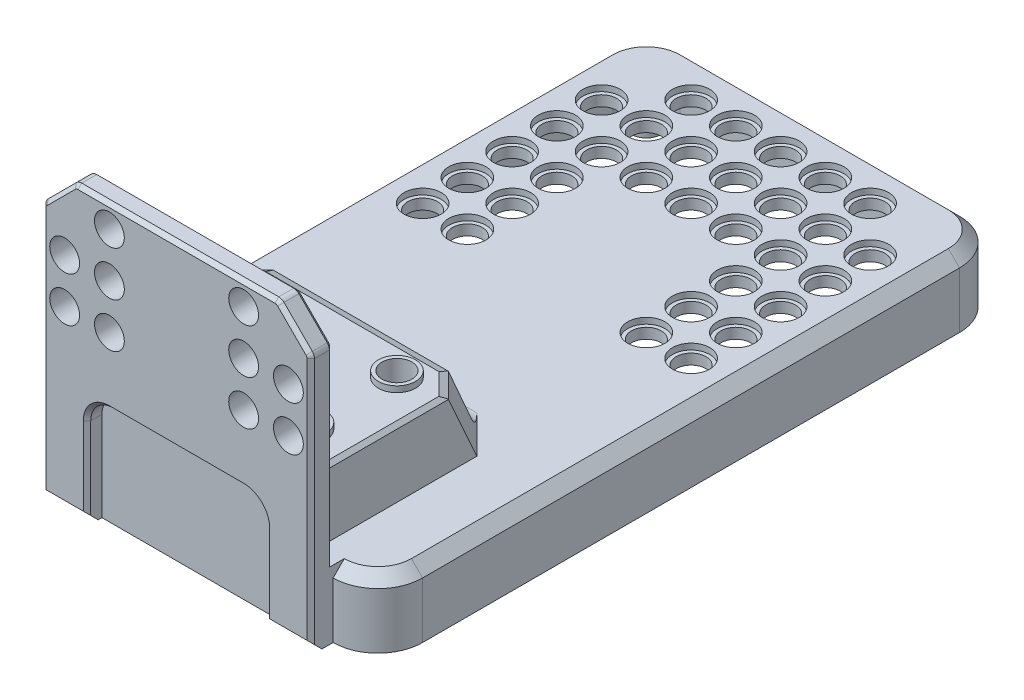
SolidWorks part; units mm, degrees
material "ABS"
ref_plane "Front Plane" through (0, 0, 0) normal (0, 0, 1) x (1, 0, 0)
ref_plane "Top Plane" through (0, 0, 0) normal (0, 1, 0) x (1, 0, 0)
ref_plane "Right Plane" through (0, 0, 0) normal (1, 0, 0) x (0, 0, -1)
sketch "Sketch1" plane through (0, 0, 0) normal (0, 1, 0) x (1, 0, 0)
  line L0 (-24, 36) -> (-24, -36)
  line L1 (-18, -42) -> (18, -42)
  line L2 (-18, 42) -> (18, 42)
  line L3 (0, -1000) -> (0, 49000) construction
  line L4 (24, 36) -> (24, -36)
  arc A0 (-24, -36) -> (-18, -42) centre (-18, -36) ccw
  arc A1 (-24, 36) -> (-18, 42) centre (-18, 36) cw
  arc A2 (24, 36) -> (18, 42) centre (18, 36) ccw
  arc A3 (24, -36) -> (18, -42) centre (18, -36) cw
  point P7 (-24, 0)
  point P9 (0, -42)
  point P18 (0, 42)
  dimension "D1" = 6
  dimension "D2" = 72
  dimension "D3" = 18
extrude "Boss-Extrude1" add sketch "Sketch1" along normal mid plane 2.2
sketch "Sketch2" plane through (0, -1.1, 0) normal (0, -1, 0) x (1, 0, 0)
  line L0 (24, 36) -> (24, -36) construction
  line L1 (18, -42) -> (-18, -42) construction
  line L2 (-24, -36) -> (-24, 36) construction
  line L3 (-18, 42) -> (18, 42) construction
  line L4 (24, 36) -> (24, -36)
  line L5 (18, -42) -> (-18, -42)
  line L6 (-24, -36) -> (-24, 36)
  line L7 (-18, 42) -> (18, 42)
  line L8 (18, -40.5) -> (-18, -40.5)
  line L9 (-22.5, -36) -> (-22.5, 36)
  line L10 (-18, 40.5) -> (18, 40.5)
  line L11 (22.5, 36) -> (22.5, -36)
  arc A0 (24, 36) -> (18, 42) centre (18, 36) ccw construction
  arc A1 (18, -42) -> (24, -36) centre (18, -36) ccw construction
  arc A2 (-24, -36) -> (-18, -42) centre (-18, -36) ccw construction
  arc A3 (-18, 42) -> (-24, 36) centre (-18, 36) ccw construction
  arc A4 (24, 36) -> (18, 42) centre (18, 36) ccw
  arc A5 (18, -42) -> (24, -36) centre (18, -36) ccw
  arc A6 (-24, -36) -> (-18, -42) centre (-18, -36) ccw
  arc A7 (-18, 42) -> (-24, 36) centre (-18, 36) ccw
  arc A8 (-18, -40.5) -> (-22.5, -36) centre (-18, -36) cw
  arc A9 (-22.5, 36) -> (-18, 40.5) centre (-18, 36) cw
  arc A10 (18, 40.5) -> (22.5, 36) centre (18, 36) cw
  arc A11 (22.5, -36) -> (18, -40.5) centre (18, -36) cw
  dimension "D1" = 1.5
extrude "Boss-Extrude2" add sketch "Sketch2" along normal blind 6.8
sketch "Sketch4" plane through (0, -1.1, 0) normal (0, -1, 0) x (1, 0, 0)
  line L1 (-18, 42) -> (18, 42) construction
  line L3 (15, 18.75) -> (12, 15.75)
  line L4 (12, 15.75) -> (-12, 15.75)
  line L5 (-12, 15.75) -> (-15, 18.75)
  line L8 (-15, 18.75) -> (-15, 42)
  line L9 (-15, 42) -> (15, 42)
  line L10 (15, 42) -> (15, 18.75)
  point P4 (0, 42)
  point P9 (0, 15.75)
  dimension "D1" = 30
  dimension "D2" = 24
  dimension "D3" = 23.25
ref_plane "Plane1" through (0, 10.1, 0) normal (0, -1, 0) x (-1, 0, 0)
sketch "Sketch5" plane through (0, 10.1, 0) normal (0, -1, 0) x (-1, 0, 0)
  line L0 (-15, -42) -> (15, -42)
  line L1 (-15, -42) -> (-15, -23.75)
  line L2 (-15, -42) -> (-15, -18.75) construction
  line L3 (-15, -23.75) -> (-11.75, -20.5)
  line L4 (-11.75, -20.5) -> (11.75, -20.5)
  line L5 (11.75, -20.5) -> (15, -23.75)
  line L6 (15, -18.75) -> (15, -42) construction
  line L7 (15, -23.75) -> (15, -42)
  line L8 (-15, -18.75) -> (-12, -15.75) construction
  line L9 (12, -15.75) -> (15, -18.75) construction
  point P16 (0, -20.5)
  point P17 (0, -42)
  dimension "D1" = 23.5
  dimension "D2" = 18.25
loft "Loft1" add profiles "Sketch4", "Sketch5"
sketch "Sketch6" plane through (0, 0, 42) normal (0, 0, 1) x (1, 0, 0)
  line L0 (18, -7.9) -> (-18, -7.9)
  line L1 (18, -7.9) -> (18, 26.725)
  line L2 (18, 26.725) -> (13.625, 31.1)
  line L3 (13.625, 31.1) -> (-13.625, 31.1)
  line L4 (-13.625, 31.1) -> (-18, 26.725)
  line L5 (-18, 26.725) -> (-18, -7.9)
  point P4 (0, 31.1)
  point P9 (0, -7.9)
  dimension "D1" = 39
  dimension "D2" = 27.25
extrude "Boss-Extrude3" add sketch "Sketch6" along normal blind 3
fillet "Fillet1" radius 1 4 edges at (-18, 26.725, 43.5) (-13.625, 31.1, 43.5) (18, 26.725, 43.5) (13.625, 31.1, 43.5)
ref_plane "Plane2" through (0, 7.9, 0) normal (0, -1, 0) x (-1, 0, 0)
sketch "Sketch7" plane through (0, 7.9, 0) normal (0, -1, 0) x (-1, 0, 0)
  line L7 (13.5, -42) -> (-13.5, -42)
  line L11 (-15, -42) -> (15, -42) construction
  line L12 (-13.2108, -42) -> (13.2108, -42) construction
  line L13 (-13.5, -42) -> (-13.5, -24.3713)
  line L14 (-13.5, -24.3713) -> (-11.1287, -22)
  line L15 (-11.1287, -22) -> (11.1287, -22)
  line L16 (11.1287, -22) -> (13.5, -24.3713)
  line L17 (13.5, -24.3713) -> (13.5, -42)
  line L18 (11.75, -20.5) -> (-11.75, -20.5) construction
  line L19 (15, -23.75) -> (11.75, -20.5) construction
  point P7 (0, -22)
  point P13 (0, -42)
  point P19 (13.375, -22.125)
  dimension "D1" = 27
  dimension "D2" = 1.5
  dimension "D3" = 1.5
sketch "Sketch8" plane through (0, -1.1, 0) normal (0, -1, 0) x (1, 0, 0)
  line L0 (13.5, 42) -> (-13.5, 42)
  line L1 (-13.5, 42) -> (-13.5, 19)
  line L2 (-13.5, 19) -> (-11.1287, 16.6287)
  line L3 (-11.1287, 16.6287) -> (11.1287, 16.6287)
  line L4 (11.1287, 16.6287) -> (13.5, 19)
  line L5 (13.5, 19) -> (13.5, 42)
  point P3 (0, 42)
  point P9 (0, 16.6287)
  dimension "D1" = 27
  dimension "D3" = 23
loft "Cut-Loft1" cut profiles "Sketch7", "Sketch8"
fillet "Fillet3" radius 3 2 edges at (0, 1.1, 16.683)
sketch "Sketch9" plane through (0, 0, 45) normal (0, 0, 1) x (1, 0, 0)
  line L0 (12, -7.9) -> (-12, -7.9)
  line L1 (-18, -7.9) -> (18, -7.9) construction
  line L2 (-12, -7.9) -> (-12, 4.1)
  line L3 (-9, 7.1) -> (9, 7.1)
  line L4 (12, 4.1) -> (12, -7.9)
  arc A0 (-12, 4.1) -> (-9, 7.1) centre (-9, 4.1) cw
  arc A1 (9, 7.1) -> (12, 4.1) centre (9, 4.1) cw
  point P10 (0, 7.1)
  point P11 (0, -7.9)
  dimension "D2" = 3
  dimension "D1" = 18
  dimension "D3" = 12
extrude "Cut-Extrude1" cut sketch "Sketch9" against normal blind 2
chamfer "Chamfer2" distance 1.5 angle 45 18 edges at (-21.182, -1.1, 39.182) (-22.5, -1.1, 0) (-21.182, -1.1, -39.182) (0, -1.1, -40.5) (21.182, -1.1, -39.182) (21.182, -1.1, 39.182) (22.5, -1.1, 0) (22.2426, 1.1, 40.2426) (24, 1.1, 0) (22.2426, 1.1, -40.2426) (0, 1.1, -42) (-22.2426, 1.1, -40.2426) (-22.2426, 1.1, 40.2426) (-24, 1.1, 0) (15, -7.9, 45) (-15, -7.9, 45)
chamfer "Chamfer3" distance 0.5 angle 45 31 edges at (12, -1.15, 45) (11.1213, 6.2213, 45) (0, 7.1, 45) (-11.1213, 6.2213, 45) (-12, -1.15, 45) (-18, 13.7054, 42) (-17.9239, 26.6935, 42) (-15.8125, 28.9125, 42) (-13.5935, 31.0239, 42) (18, 13.7054, 42) (0, 31.1, 42) (17.9239, 26.6935, 42) (13.5935, 31.0239, 42) (15.8125, 28.9125, 42) (18, 9.9554, 45) (-18, 9.9554, 45) (17.9239, 26.6935, 45) (-17.9239, 26.6935, 45) (15.8125, 28.9125, 45) (-15.8125, 28.9125, 45) (13.5935, 31.0239, 45) (-13.5935, 31.0239, 45) (0, 31.1, 45)
sketch "Sketch10" plane through (0, 0, 42) normal (0, 0, -1) x (-1, 0, 0)
  line L0 (14.5, 10.1) -> (-14.5, 10.1) construction
  line L1 (-18, 1.1) -> (-18, 26.3108) construction
  circle A0 centre (-15, 16.1) radius 2
  circle A1 centre (-9, 16.1) radius 2
  circle A2 centre (-3, 16.1) radius 2 [skipped]
  circle A3 centre (3, 16.1) radius 2 [skipped]
  circle A4 centre (9, 16.1) radius 2
  circle A5 centre (15, 16.1) radius 2
  circle A6 centre (-9, 22.1) radius 2
  circle A7 centre (-3, 22.1) radius 2 [skipped]
  circle A8 centre (3, 22.1) radius 2 [skipped]
  circle A9 centre (9, 22.1) radius 2
  circle A10 centre (15, 22.1) radius 2
  circle A11 centre (-9, 28.1) radius 2
  circle A12 centre (-3, 28.1) radius 2 [skipped]
  circle A13 centre (3, 28.1) radius 2 [skipped]
  circle A14 centre (9, 28.1) radius 2
  circle A15 centre (15, 28.1) radius 2 [skipped]
  circle A16 centre (-15, 22.1) radius 2
  circle A17 centre (-15, 28.1) radius 2 [skipped]
  dimension "D1" = 4
  dimension "D2" = 6
  dimension "D3" = 3
  dimension "D4" = 6
  dimension "D6" = 6
  dimension "D7" = 6
  dimension "D8" = 90
  dimension "D5" = 3
extrude "Cut-Extrude2" cut sketch "Sketch10" against normal through all
sketch "Sketch11" plane through (0, 1.1, 0) normal (0, 1, 0) x (1, 0, 0)
  line L0 (24, 36) -> (24, -36) construction
  line L1 (-18, 42) -> (18, 42) construction
  circle A0 centre (18, 6) radius 2
  dimension "D1" = 4
  dimension "D2" = 6
  dimension "D3" = 36
extrude "Cut-Extrude3" cut sketch "Sketch11" against normal through all
sketch "Sketch12" plane through (0, 1.1, 0) normal (0, 1, 0) x (1, 0, 0)
  circle A0 centre (18, 6) radius 2.5
  dimension "D1" = 5
extrude "Cut-Extrude4" cut sketch "Sketch12" against normal blind 0.8
pattern_linear "LPattern1" count 7 spacing 6 along (-1, 0, 0) count 6 spacing 6 along (0, 0, -1) skipping (0, 5), (2, 0), (2, 1), (2, 2), (3, 0), (3, 1), (3, 2), (4, 0), (4, 1), (4, 2), (6, 5) of "Cut-Extrude3", "Cut-Extrude4"
sketch "Sketch13" plane through (0, 10.1, 0) normal (0, 1, 0) x (1, 0, 0)
  line L0 (15, -23.5268) -> (15, -41.5) construction
  line L1 (11.6095, -21.4431) -> (-11.6095, -21.4431) construction
  circle A0 centre (9.5, -24.9431) radius 2
  dimension "D1" = 4
  dimension "D2" = 5.5
  dimension "D3" = 3.5
extrude "Cut-Extrude5" cut sketch "Sketch13" against normal through all
sketch "Sketch14" plane through (0, 10.1, 0) normal (0, 1, 0) x (1, 0, 0)
  circle A0 centre (9.5, -24.9431) radius 2.5
  circle A1 centre (9.5, -24.9431) radius 2 construction
  circle A2 centre (9.5, -24.9431) radius 2
  dimension "D1" = 5
extrude "Boss-Extrude5" add sketch "Sketch14" along normal blind 0.8
pattern_linear "LPattern5" count 2 spacing 19 along (-1, 0, 0) count 2 spacing 12 along (0, 0, 1) of "Boss-Extrude5", "Cut-Extrude5"
sketch "Sketch15" plane through (0, -1.1, 0) normal (0, -1, 0) x (1, 0, 0)
  circle A0 centre (18, -36) radius 2
  circle A1 centre (12, -36) radius 2 construction
  circle A2 centre (12, -36) radius 2 construction
  circle A3 centre (18, -30) radius 2 construction
  circle A4 centre (18, -30) radius 2 construction
  circle A5 centre (18, -36) radius 0.8
  dimension "D1" = 4
  dimension "D2" = 1.6
extrude "Boss-Extrude4" add sketch "Sketch15" along normal blind 3.8
pattern_linear "LPattern4" count 2 spacing 72 along (0, 0, 1) count 2 spacing 36 along (-1, 0, 0) of "Boss-Extrude4"
